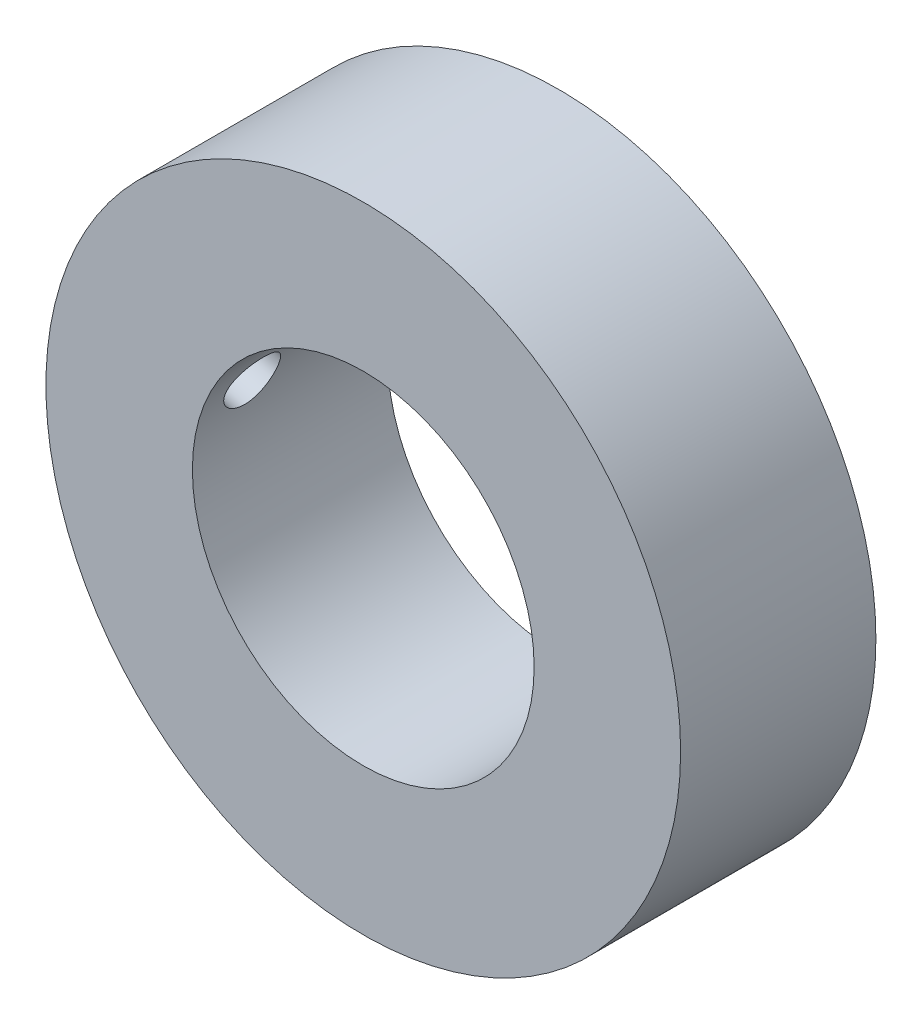
SolidWorks part; units mm, degrees
ref_plane "Ebene vorne" through (0, 0, 0) normal (0, 0, 1) x (1, 0, 0)
ref_plane "Ebene oben" through (0, 0, 0) normal (0, 1, 0) x (1, 0, 0)
ref_plane "Ebene rechts" through (0, 0, 0) normal (1, 0, 0) x (0, 0, -1)
sketch "Skizze1" plane through (0, 0, 0) normal (0, 0, 1) x (1, 0, 0)
  circle A0 centre (0, 0) radius 17.5
  circle A1 centre (0, 0) radius 32.5
  dimension "D1" = 35
  dimension "D2" = 65
extrude "Aufsatz-Linear austragen1" add sketch "Skizze1" along normal blind 20
sketch "Skizze2" plane through (0, 0, 20) normal (0, 0, 1) x (1, 0, 0)
  line L0 (-30.9233, 10) -> (31.7804, -6.8014) construction
  line L1 (0, 0) -> (-46.465, 0) construction
  circle A0 centre (0, 0) radius 32.5 construction
  circle A1 centre (0, 0) radius 17.5 construction
  dimension "D1" = 15
  dimension "D2" = 10
ref_plane "Ebene1" through (-30.9233, 10, 20) normal (0.9659, -0.2588, 0) x (0, 0, -1)
ref_plane "Ebene2" through (-41.0111, 10.9889, 0) normal (0.9659, -0.2588, 0) x (0, 0, -1)
hole_wizard "Ø5.5 (5.5) Durchmesser Bohrung2" positions "Skizze4" profile "Skizze3" hole size "Ø5.5" standard "RSG Norm"
sketch "Skizze4" plane through (-51.2111, -27.078, 64.7936) normal (0.9659, -0.2588, 0) x (0, 0, -1)
  line L0 (44.7936, 41.0654) -> (64.7936, 41.0654) construction
  line L2 (64.7936, 6.9097) -> (64.7936, 71.9097) construction
  line L3 (44.7936, 71.9097) -> (44.7936, 6.9097) construction
  point P1 (49.7936, 41.0654)
  dimension "D1" = 5
sketch "Skizze3" plane through (-40.5826, 12.5882, 15) normal (0, 0, 1) x (-0.2588, -0.9659, 0)
  line L0 (0, 0) -> (0, 25.0363)
  line L1 (0, 25.0363) -> (2.75, 25.0363)
  line L2 (2.75, 25.0363) -> (2.75, 0)
  line L5 (2.75, 0) -> (0, 0)
  line L11 (0, -6.35) -> (0, 107.95) construction
  dimension "Bohrerdurchmesser" = 5.5
  dimension "Bohrungstiefe" = 25.0363
